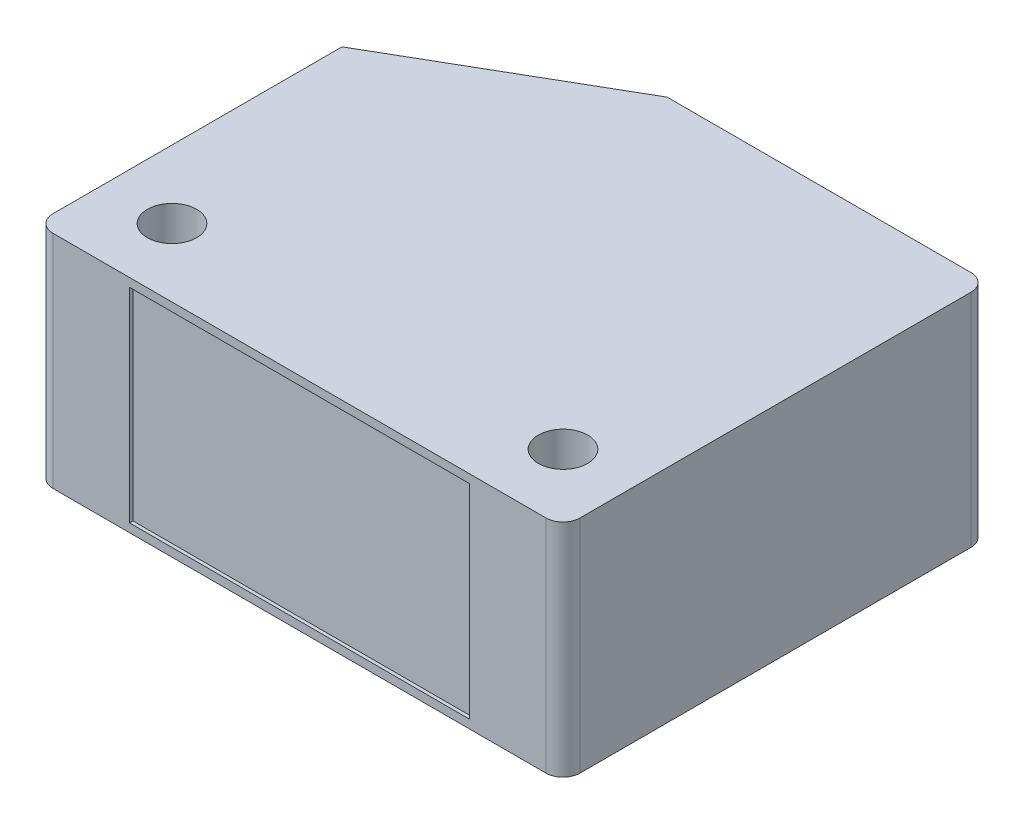
SolidWorks part; units mm, degrees
ref_plane "Front Plane" through (0, 0, 0) normal (0, 0, 1) x (1, 0, 0)
ref_plane "Top Plane" through (0, 0, 0) normal (0, 1, 0) x (1, 0, 0)
ref_plane "Right Plane" through (0, 0, 0) normal (1, 0, 0) x (0, 0, -1)
sketch "Sketch1" plane through (0, 0, 0) normal (0, 1, 0) x (1, 0, 0)
  line L1 (-15.5, 11.0605) -> (15.5, 11.0605)
  line L2 (-15.5, 11.0605) -> (-15.5, -13.9395)
  line L3 (-15.5, -13.9395) -> (15.5, -13.9395)
  line L4 (15.5, 11.0605) -> (15.5, -13.9395)
  circle A0 centre (-11.5, -9.9395) radius 1.45
  circle A1 centre (11.5, -9.9395) radius 1.45
  point P0 (0, 0)
  dimension "D3" = 2.9
  dimension "D4" = 2.9
  dimension "D1" = 31
  dimension "D2" = 25
  dimension "D5" = 4
  dimension "D6" = 4
  dimension "D7" = 4
  dimension "D8" = 4
extrude "Boss-Extrude1" add sketch "Sketch1" along normal blind 13
sketch "Sketch2" plane through (0, 0, 13.9395) normal (0, 0, 1) x (1, 0, 0)
  line L0 (-15.5, 0) -> (15.5, 0) construction
  line L1 (-10, 12.5) -> (10, 12.5)
  line L2 (-10, 12.5) -> (-10, 0.5)
  line L3 (-10, 0.5) -> (10, 0.5)
  line L4 (10, 12.5) -> (10, 0.5)
  line L5 (-10, 12.5) -> (10, 0.5) construction
  line L6 (-10, 0.5) -> (10, 12.5) construction
  line L7 (-15.5, 13) -> (15.5, 13) construction
  point P0 (0, 6.5)
  dimension "D1" = 20
  dimension "D2" = 0.5
  dimension "D3" = 0.5
extrude "Cut-Extrude1" cut sketch "Sketch2" against normal blind 0.2
sketch "Sketch3" plane through (0, 13, 0) normal (0, 1, 0) x (1, 0, 0)
  line L0 (-15.5, 4.0605) -> (-3.3756, 11.0605)
  line L1 (-15.5, 11.0605) -> (-15.5, -13.9395) construction
  line L2 (15.5, 11.0605) -> (-15.5, 11.0605) construction
  line L3 (-3.3756, 11.0605) -> (-15.5, 11.0605)
  line L4 (-15.5, 11.0605) -> (-15.5, 4.0605)
  line L5 (-15.5, 4.0605) -> (-1.8478, 4.0605) construction
  dimension "D1" = 30
  dimension "D2" = 7
extrude "Cut-Extrude2" cut sketch "Sketch3" against normal through all
fillet "Fillet1" radius 1 3 edges at (-15.5, 6.5, 13.9395) (15.5, 6.5, -11.0605) (15.5, 6.5, 13.9395)
